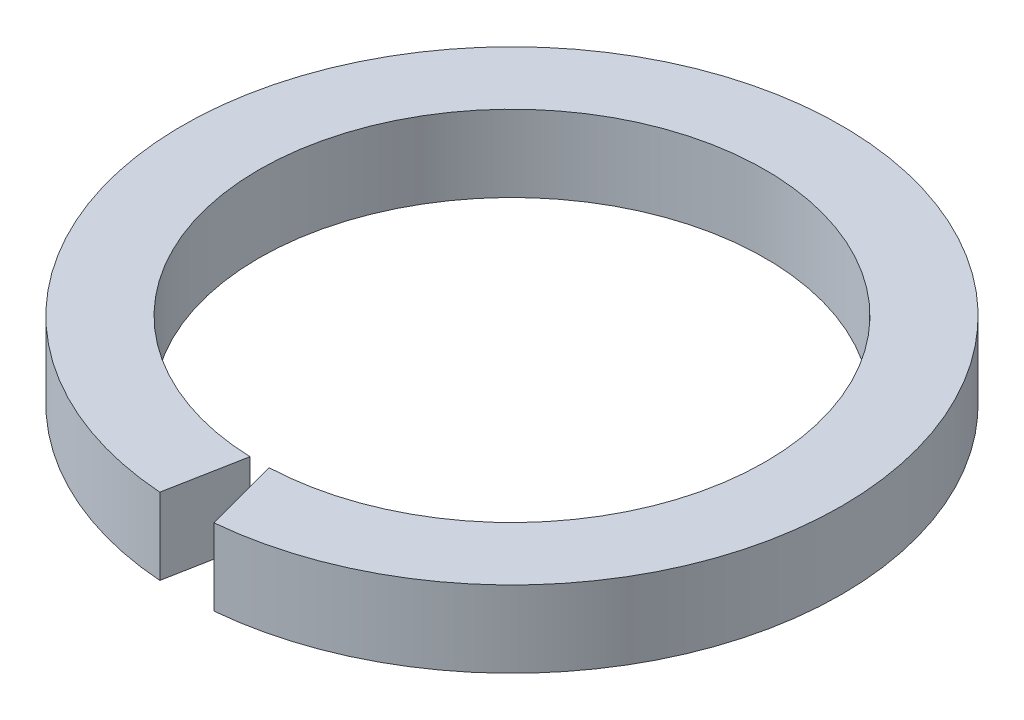
SolidWorks part; units mm, degrees
ref_plane "Front Plane" through (0, 0, 0) normal (0, 0, 1) x (1, 0, 0)
ref_plane "Top Plane" through (0, 0, 0) normal (0, 1, 0) x (1, 0, 0)
ref_plane "Right Plane" through (0, 0, 0) normal (1, 0, 0) x (0, 0, -1)
sketch "Sketch1" plane through (0, 0, 0) normal (0, 1, 0) x (1, 0, 0)
  circle A0 centre (0, 0) radius 16.55
  circle A1 centre (0, 0) radius 21.55
extrude "Boss-Extrude1" add sketch "Sketch1" along normal blind 5
sketch "Sketch3" plane through (0, 0, 0) normal (0, 1, 0) x (1, 0, 0)
  line L0 (0, 0) -> (0, -27.1481) construction
  line L1 (-1.7584, -22.6892) -> (2.3055, -22.6892)
  line L2 (0, -15.9931) -> (-0.4889, -15.9931)
  line L3 (0, -15.9931) -> (0.5048, -15.9931)
  line L4 (0.5048, -15.9931) -> (2.3055, -22.6892)
  line L5 (-1.7584, -22.6892) -> (-0.4889, -15.9931)
extrude "Cut-Extrude2" cut sketch "Sketch3" against normal blind 12 and the other way blind 15
